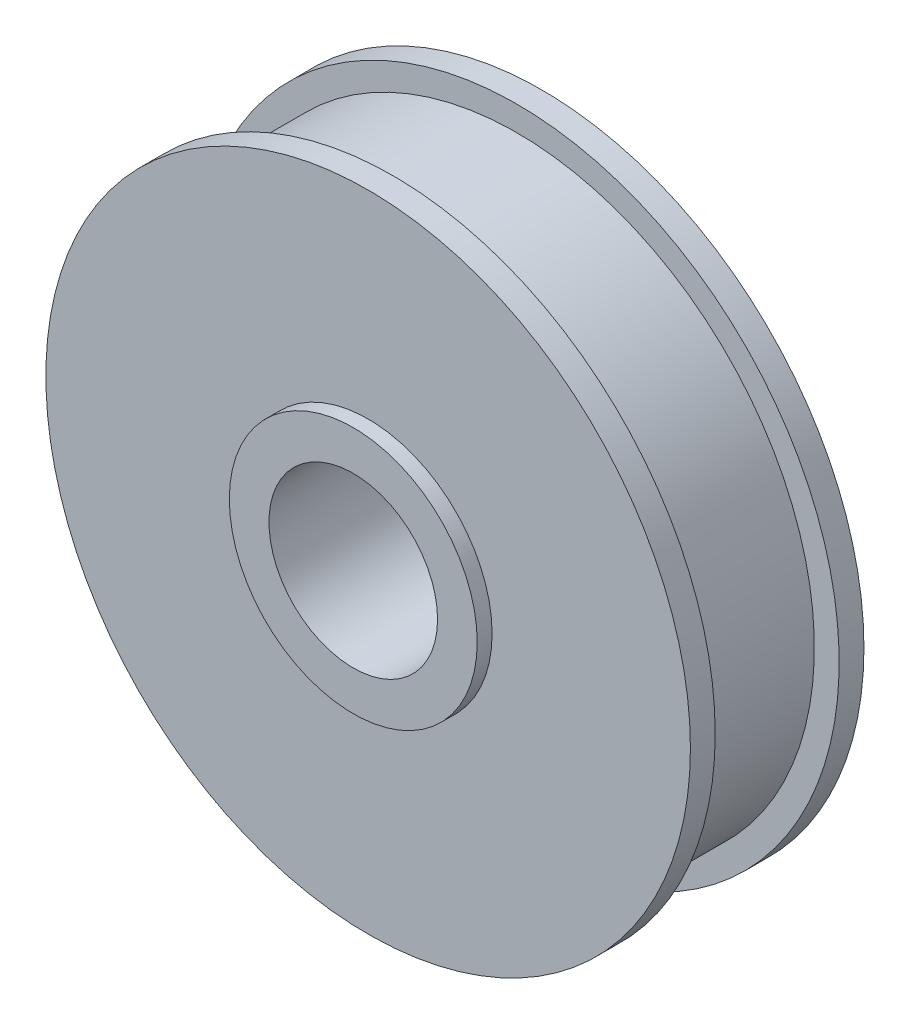
SolidWorks part; units mm, degrees
ref_plane "Front Plane" through (0, 0, 0) normal (0, 0, 1) x (1, 0, 0)
ref_plane "Top Plane" through (0, 0, 0) normal (0, 1, 0) x (1, 0, 0)
ref_plane "Right Plane" through (0, 0, 0) normal (1, 0, 0) x (0, 0, -1)
sketch "Sketch1" plane through (0, 0, 0) normal (0, 0, 1) x (1, 0, 0)
  circle A0 centre (0, 0) radius 6.5
  dimension "D1" = 13
extrude "Boss-Extrude1" add sketch "Sketch1" along normal blind 3.5
sketch "Sketch2" plane through (0, 0, 3.5) normal (0, 0, 1) x (1, 0, 0)
  circle A0 centre (0, 0) radius 2.5
  dimension "D1" = 5
extrude "Boss-Extrude2" add sketch "Sketch2" along normal blind 0.3
ref_plane "Plane1" through (0, 0, 0.5) normal (0, 0, -1) x (-1, 0, 0)
sketch "Sketch3" plane through (0, 0, 0.5) normal (0, 0, -1) x (-1, 0, 0)
  circle A0 centre (0, 0) radius 6
  circle A1 centre (0, 0) radius 6.5
  circle A2 centre (0, 0) radius 6.5
  dimension "D2" = 0.5
  dimension "D1" = 0
extrude "Cut-Extrude1" cut sketch "Sketch3" against normal offset from surface (2.5 mm away) 0.5 up to face at (6.5, 0, 3.5)
sketch "Sketch4" plane through (0, 0, 3.8) normal (0, 0, 1) x (1, 0, 0)
  circle A0 centre (0, 0) radius 1.7
  dimension "D1" = 3.4
extrude "Cut-Extrude2" cut sketch "Sketch4" against normal through all contours A0
